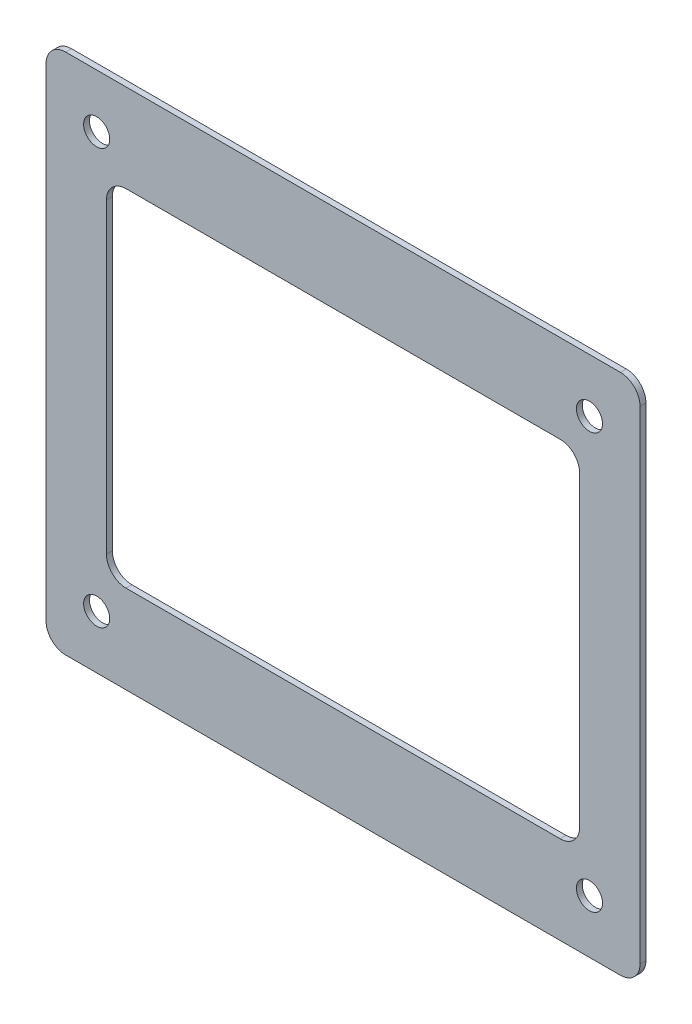
SolidWorks part; units mm, degrees
ref_plane "Alzado" through (0, 0, 0) normal (0, 0, 1) x (1, 0, 0)
ref_plane "Planta" through (0, 0, 0) normal (0, 1, 0) x (1, 0, 0)
ref_plane "Vista lateral" through (0, 0, 0) normal (1, 0, 0) x (0, 0, -1)
sketch "Croquis1" plane through (0, 0, 0) normal (0, 0, 1) x (1, 0, 0)
  line L0 (-45.324, 37.2641) -> (-45.324, -36.7359)
  line L1 (-42.324, -39.7359) -> (42.676, -39.7359)
  line L2 (45.676, -36.7359) -> (45.676, 37.2641)
  line L3 (42.676, 40.2641) -> (-42.324, 40.2641)
  line L4 (-33.074, -26.2359) -> (33.426, -26.2359)
  line L5 (-36.074, 23.7641) -> (-36.074, -23.2359)
  line L6 (36.426, -23.2359) -> (36.426, 23.7641)
  line L7 (33.426, 26.7641) -> (-33.074, 26.7641)
  arc A0 (-45.324, -36.7359) -> (-42.324, -39.7359) centre (-42.324, -36.7359) ccw
  arc A1 (42.676, -39.7359) -> (45.676, -36.7359) centre (42.676, -36.7359) ccw
  arc A2 (45.676, 37.2641) -> (42.676, 40.2641) centre (42.676, 37.2641) ccw
  arc A3 (-42.324, 40.2641) -> (-45.324, 37.2641) centre (-42.324, 37.2641) ccw
  circle A4 centre (-37.574, 32.0641) radius 2
  circle A5 centre (37.926, 32.0641) radius 2
  circle A6 centre (37.926, -31.5359) radius 2
  circle A7 centre (-37.574, -31.5359) radius 2
  arc A8 (33.426, -26.2359) -> (36.426, -23.2359) centre (33.426, -23.2359) ccw
  arc A9 (-36.074, -23.2359) -> (-33.074, -26.2359) centre (-33.074, -23.2359) ccw
  arc A10 (36.426, 23.7641) -> (33.426, 26.7641) centre (33.426, 23.7641) ccw
  arc A11 (-33.074, 26.7641) -> (-36.074, 23.7641) centre (-33.074, 23.7641) ccw
extrude "Saliente-Extruir1" add sketch "Croquis1" along normal blind 0.9
